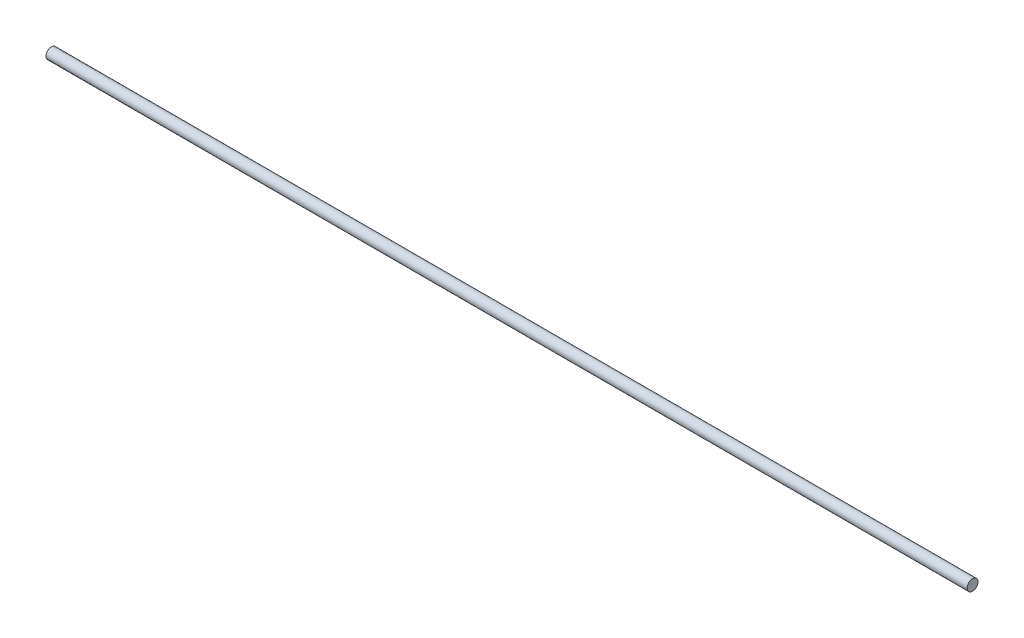
SolidWorks part; units mm, degrees
ref_plane "Front Plane" through (0, 0, 0) normal (0, 0, 1) x (1, 0, 0)
ref_plane "Top Plane" through (0, 0, 0) normal (0, 1, 0) x (1, 0, 0)
ref_plane "Right Plane" through (0, 0, 0) normal (1, 0, 0) x (0, 0, -1)
sketch "Sketch1" plane through (0, 0, 0) normal (1, 0, 0) x (0, 0, -1)
  circle A0 centre (0, 0) radius 2
  dimension "D1" = 4
extrude "Boss-Extrude1" add sketch "Sketch1" along normal blind 340
